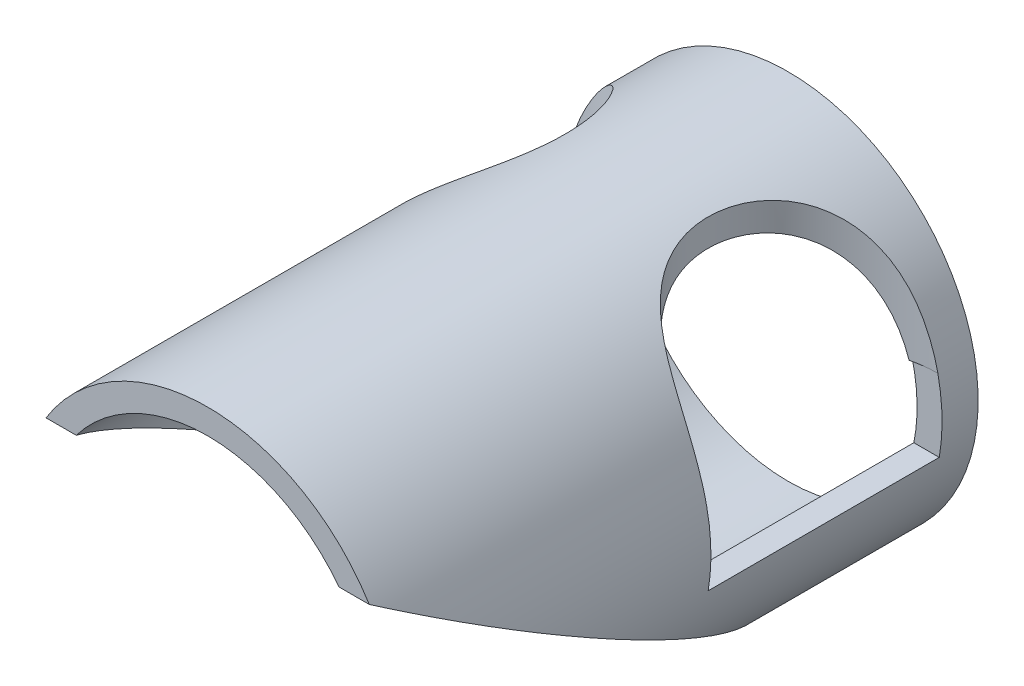
SolidWorks part; units mm, degrees
material "PVC Rigid"
ref_plane "Front Plane" through (0, 0, 0) normal (0, 0, 1) x (1, 0, 0)
ref_plane "Top Plane" through (0, 0, 0) normal (0, 1, 0) x (1, 0, 0)
ref_plane "Right Plane" through (0, 0, 0) normal (1, 0, 0) x (0, 0, -1)
sketch "Sketch1" plane through (0, 0, 0) normal (0, 0, 1) x (1, 0, 0)
  circle A0 centre (0, 0) radius 83.4771
  circle A2 centre (0, 0) radius 72.5043
  point P3 (0, 0)
  point P10 (0, 0)
  dimension "D1" = 10.9728
  dimension "D2" = 145.0086
extrude "Boss-Extrude1" add sketch "Sketch1" along normal mid plane 130.175
sketch "Sketch3" plane through (0, 0, 0) normal (1, 0, 0) x (0, 0, -1)
  line L0 (-65.0875, 83.4771) -> (-65.0875, -83.4771) construction
  line L1 (61.9125, 14.2875) -> (-39.6875, 14.2875) construction
  line L2 (61.9125, 14.2875) -> (61.9125, -14.2875)
  line L3 (61.9125, -14.2875) -> (-39.6875, -14.2875)
  line L4 (-39.6875, 14.2875) -> (-39.6875, -14.2875)
  line L5 (61.9125, 14.2875) -> (-39.6875, -14.2875) construction
  line L6 (61.9125, -14.2875) -> (-39.6875, 14.2875) construction
  line L7 (-39.6875, 14.2875) -> (0, 0) construction
  line L8 (0, 0) -> (-39.6875, -14.2875) construction
  line L9 (61.9125, 14.2875) -> (-39.6875, 14.2875)
  point P0 (11.1125, 0)
  dimension "D1" = 25.4
  dimension "D2" = 101.6
  dimension "D3" = 28.575
extrude "Cut-Extrude2" cut sketch "Sketch3" against normal through all both and the other way through all
sketch "Sketch4" plane through (0, -14.2875, 0) normal (0, 1, 0) x (1, 0, 0)
  line L0 (-71.0826, 11.1125) -> (-82.2453, 11.1125) construction
  line L1 (-71.0826, -39.6875) -> (-71.0826, 61.9125) construction
  line L2 (71.0826, 11.1125) -> (82.2453, 11.1125) construction
  line L3 (71.0826, 61.9125) -> (71.0826, -39.6875) construction
  line L4 (-82.2453, -39.6875) -> (-82.2453, 61.9125) construction
  circle A0 centre (-82.2453, 11.1125) radius 50.8
  circle A1 centre (82.2453, 11.1125) radius 50.8
  dimension "D2" = 101.6
extrude "Cut-Extrude3" cut sketch "Sketch4" along normal through all
sketch "Sketch6" plane through (0, 0, 0) normal (1, 0, 0) x (0, 0, -1)
  line L0 (61.9125, 14.2875) -> (61.9125, -14.2875) construction
  line L1 (-39.6875, 14.2875) -> (61.9125, 14.2875)
  line L2 (-39.6875, 14.2875) -> (-39.6875, 17.4625)
  line L3 (-39.6875, 17.4625) -> (61.9125, 17.4625)
  line L4 (61.9125, 14.2875) -> (61.9125, 17.4625)
  line L5 (-39.6875, -14.2875) -> (-39.6875, 14.2875) construction
  line L9 (-39.6875, 14.2875) -> (-38.4459, 14.2875) construction
  dimension "D1" = 3.175
extrude "Cut-Extrude4" cut sketch "Sketch6" against normal through all both and the other way through all
sketch "Sketch9" plane through (0, 0, 65.0875) normal (0, 0, 1) x (1, 0, 0)
  circle A0 centre (0, 0) radius 72.5043 construction
  circle A1 centre (0, 0) radius 83.4771 construction
  circle A2 centre (0, 0) radius 72.5043
  circle A3 centre (0, 0) radius 83.4771
extrude "Boss-Extrude2" add sketch "Sketch9" along normal blind 508
sketch "Sketch12" plane through (0, 0, 0) normal (0, 1, 0) x (1, 0, 0)
  line L0 (152.4, -101.6) -> (-152.4, -101.6) construction
  point P3 (0, -101.6)
  dimension "D1" = 304.8
  dimension "D2" = 101.6
ref_plane "Plane5" through (0, -43.9941, 25.4) normal (0, 0.866, -0.5) x (-1, 0, 0)
sketch "Sketch13" plane through (0, -43.9941, 25.4) normal (0, 0.866, -0.5) x (-1, 0, 0)
  line L1 (-101.6, -928.0118) -> (101.6, -928.0118)
  line L2 (-101.6, -928.0118) -> (-101.6, 1103.9882)
  line L3 (-101.6, 1103.9882) -> (101.6, 1103.9882)
  line L4 (101.6, -928.0118) -> (101.6, 1103.9882)
  line L5 (-101.6, -928.0118) -> (101.6, 1103.9882) construction
  line L6 (-101.6, 1103.9882) -> (101.6, -928.0118) construction
  point P0 (0, 87.9882)
  dimension "D1" = 2032
  dimension "D2" = 203.2
extrude "Cut-Extrude7" cut sketch "Sketch13" against normal blind 762
ref_plane "Plane8" through (0, 0, 177.4825) normal (0, 0, -1) x (-1, 0, 0)
sketch "Sketch15" plane through (0, 0, 177.4825) normal (0, 0, -1) x (-1, 0, 0)
  line L1 (101.6, 101.6) -> (-101.6, 101.6)
  line L2 (101.6, 101.6) -> (101.6, -101.6)
  line L3 (101.6, -101.6) -> (-101.6, -101.6)
  line L4 (-101.6, 101.6) -> (-101.6, -101.6)
  line L5 (101.6, 101.6) -> (-101.6, -101.6) construction
  line L6 (101.6, -101.6) -> (-101.6, 101.6) construction
  point P0 (0, 0)
  dimension "D1" = 203.2
  dimension "D2" = 203.2
extrude "Cut-Extrude9" cut sketch "Sketch15" against normal blind 203.2 contours L1 L4 L3 L2
sketch "Sketch16" plane through (0, 0, -65.0875) normal (0, 0, -1) x (-1, 0, 0)
  circle A0 centre (0, 0) radius 72.5043 construction
  circle A1 centre (0, 0) radius 83.4771 construction
  circle A2 centre (0, 0) radius 72.5043
  circle A3 centre (0, 0) radius 83.4771
extrude "Boss-Extrude3" add sketch "Sketch16" along normal blind 12.7
